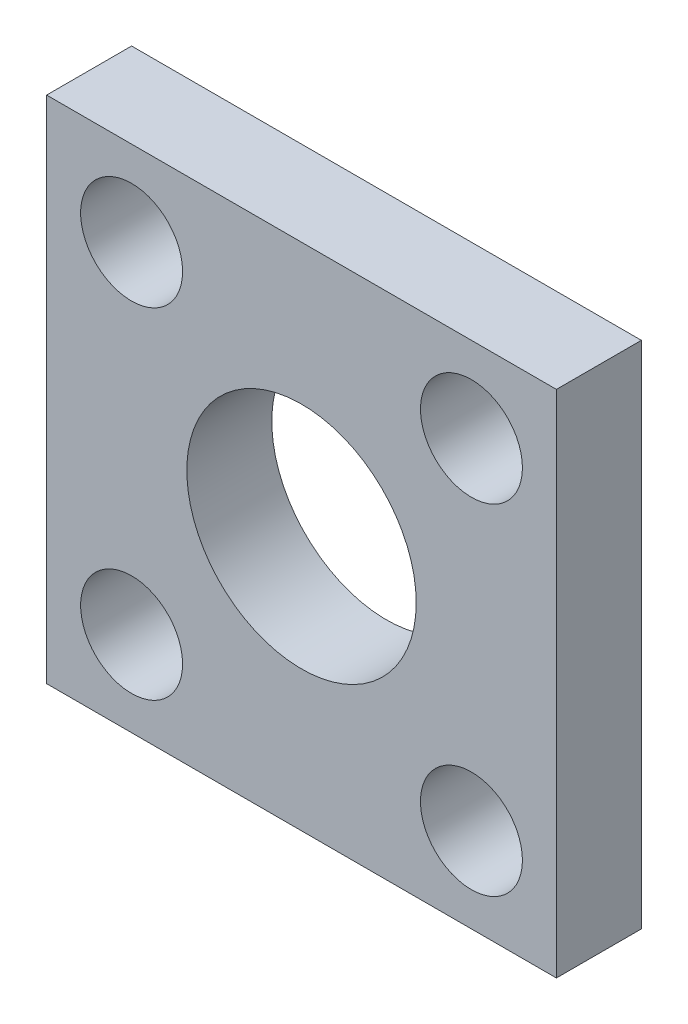
SolidWorks part; units mm, degrees
ref_plane "Ön Düzlem" through (0, 0, 0) normal (0, 0, 1) x (1, 0, 0)
ref_plane "Üst Düzlem" through (0, 0, 0) normal (0, 1, 0) x (1, 0, 0)
ref_plane "Sağ Düzlem" through (0, 0, 0) normal (1, 0, 0) x (0, 0, -1)
sketch "Çizim1" plane through (0, 0, 0) normal (0, 0, 1) x (1, 0, 0)
  line L0 (-20, -20) -> (20, -20) construction
  line L1 (-20, -20) -> (-20, 20) construction
  line L2 (-20, 20) -> (20, 20) construction
  line L3 (20, -20) -> (20, 20) construction
  line L4 (-20, -20) -> (20, 20) construction
  line L5 (-20, 20) -> (20, -20) construction
  line L6 (-30, -30) -> (30, -30)
  line L7 (-30, -30) -> (-30, 30)
  line L8 (-30, 30) -> (30, 30)
  line L9 (30, -30) -> (30, 30)
  line L10 (-30, -30) -> (30, 30) construction
  line L11 (-30, 30) -> (30, -30) construction
  circle A0 centre (0, 0) radius 13.5
  circle A1 centre (20, 20) radius 6
  circle A2 centre (-20, 20) radius 6
  circle A3 centre (20, -20) radius 6
  circle A4 centre (-20, -20) radius 6
  dimension "D1" = 27
  dimension "D3" = 12
  dimension "D2" = 40
  dimension "D4" = 60
extrude "Yükseklik-Ekstrüzyon1" add sketch "Çizim1" along normal blind 10
